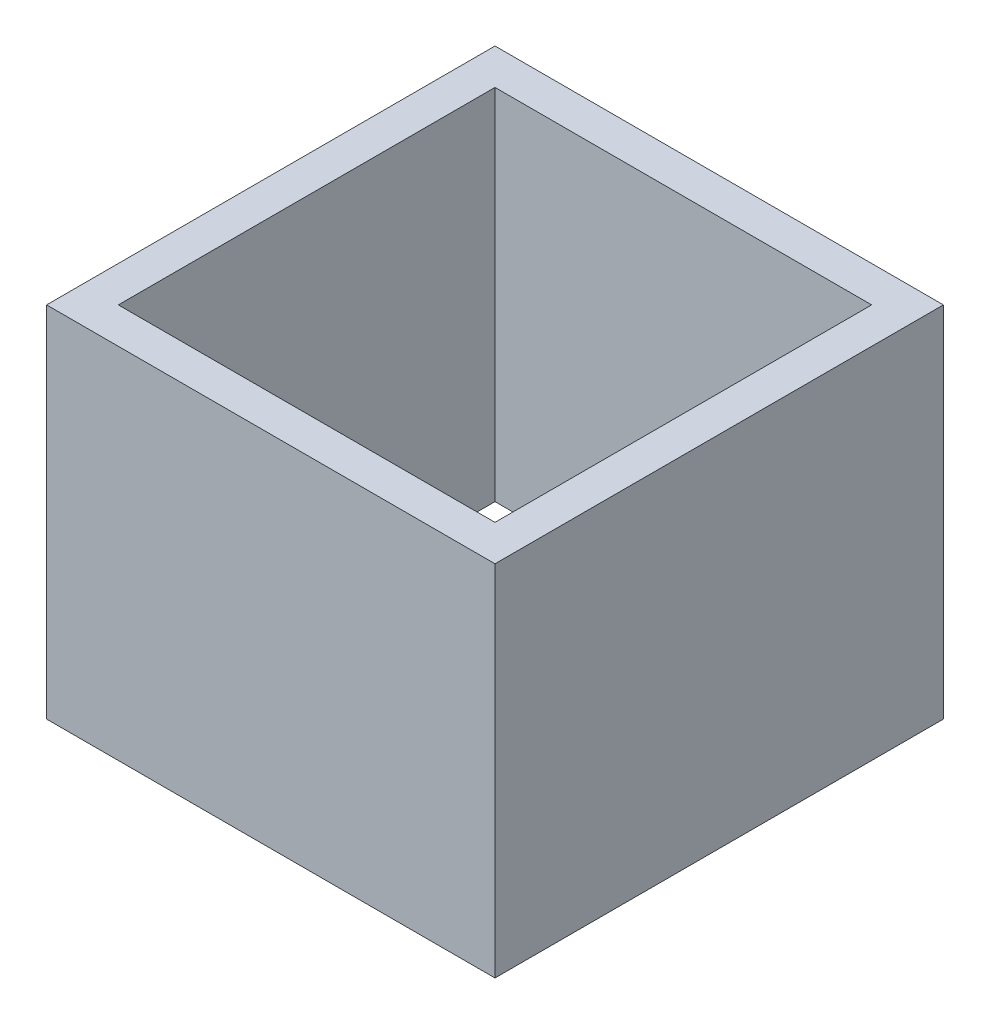
SolidWorks part; units mm, degrees
ref_plane "Спереди" through (0, 0, 0) normal (0, 0, 1) x (1, 0, 0)
ref_plane "Сверху" through (0, 0, 0) normal (0, 1, 0) x (1, 0, 0)
ref_plane "Справа" through (0, 0, 0) normal (1, 0, 0) x (0, 0, -1)
sketch "Эскиз1" plane through (0, 0, 0) normal (0, 1, 0) x (1, 0, 0)
  line L1 (-12.5, -12.5) -> (12.5, -12.5)
  line L2 (-12.5, -12.5) -> (-12.5, 12.5)
  line L3 (-12.5, 12.5) -> (12.5, 12.5)
  line L4 (12.5, -12.5) -> (12.5, 12.5)
  line L5 (-12.5, -12.5) -> (12.5, 12.5) construction
  line L6 (-12.5, 12.5) -> (12.5, -12.5) construction
  point P0 (0, 0)
extrude "Вытянуть-Тонкостенный1" add sketch "Эскиз1" along normal blind 20 thin thin type one direction reverse wall 2
